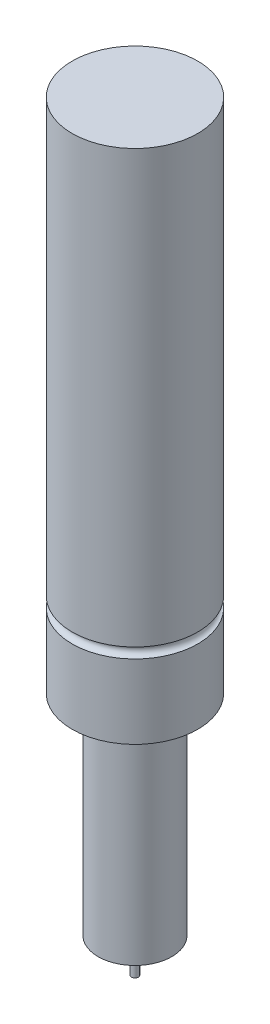
SolidWorks part; units mm, degrees
ref_plane "Plan de face" through (0, 0, 0) normal (0, 0, 1) x (1, 0, 0)
ref_plane "Plan de dessus" through (0, 0, 0) normal (0, 1, 0) x (1, 0, 0)
ref_plane "Plan de droite" through (0, 0, 0) normal (1, 0, 0) x (0, 0, -1)
sketch "Esquisse1" plane through (0, 0, 0) normal (0, 1, 0) x (1, 0, 0)
  circle A0 centre (0, 0) radius 10.7
  dimension "D1" = 21.4
extrude "Boss.-Extru.1" add sketch "Esquisse1" against normal blind 61
sketch "Esquisse2" plane through (0, 0, 0) normal (0, 1, 0) x (1, 0, 0)
  circle A0 centre (0, 0) radius 18.25
  dimension "D1" = 36.5
extrude "Boss.-Extru.2" add sketch "Esquisse2" along normal blind 150
sketch "Esquisse3" plane through (0, -61, 0) normal (0, -1, 0) x (1, 0, 0)
  circle A0 centre (0, 0) radius 1
  dimension "D1" = 2
extrude "Boss.-Extru.3" add sketch "Esquisse3" along normal blind 10
sketch "Esquisse4" plane through (0, 0, 0) normal (0, 0, 1) x (1, 0, 0)
  line L0 (18.25, 0) -> (18.25, 150) construction
  line L1 (20.075, 0) -> (-20.075, 0) construction
  line L2 (18.25, 21.5) -> (18.25, 24.5)
  arc A0 (18.25, 24.5) -> (18.25, 21.5) centre (18.25, 23) ccw
  dimension "D1" = 1.5
  dimension "D2" = 23
revolve "Enlèvement de matière-Révolution1" cut sketch "Esquisse4" angle 360 about axis through (0, 150, 0) along (0, -1, 0)
